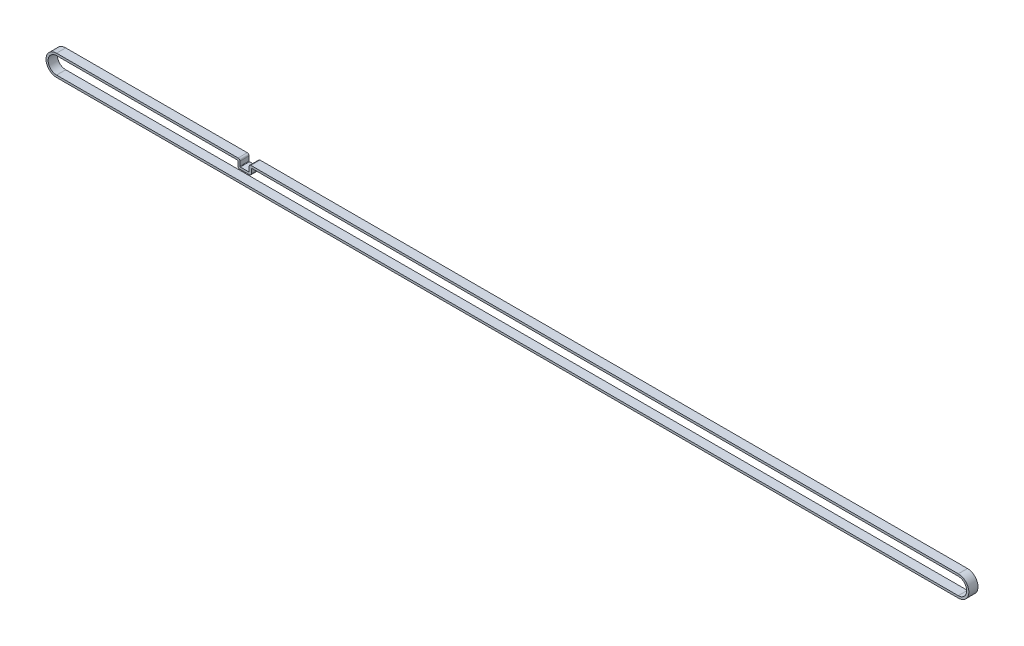
SolidWorks part; units mm, degrees
material "aluminio"
ref_plane "Alzado" through (0, 0, 0) normal (0, 0, 1) x (1, 0, 0)
ref_plane "Planta" through (0, 0, 0) normal (0, 1, 0) x (1, 0, 0)
ref_plane "Vista lateral" through (0, 0, 0) normal (1, 0, 0) x (0, 0, -1)
sketch "Croquis1" plane through (0, 0, 0) normal (0, 0, 1) x (1, 0, 0)
  line L0 (0, 0) -> (590, 0) construction
  line L1 (0, 5.5) -> (118.6, 5.5)
  line L2 (0, -5.5) -> (590, -5.5)
  line L3 (0, 6.9) -> (120, 6.9)
  line L4 (0, -6.9) -> (590, -6.9)
  line L5 (120, 6.9) -> (120, 2.5)
  line L6 (120, 2.5) -> (126, 2.5)
  line L7 (126, 2.5) -> (126, 6.9)
  line L8 (118.6, 5.5) -> (118.6, 1.1)
  line L9 (118.6, 1.1) -> (127.4, 1.1)
  line L10 (127.4, 1.1) -> (127.4, 5.5)
  line L11 (120, 5.5) -> (120, 2.5) construction
  line L12 (127.4, 5.5) -> (590, 5.5)
  line L13 (0, 5.5) -> (590, 5.5) construction
  line L14 (126, 2.5) -> (126, 5.5) construction
  line L15 (126, 6.9) -> (590, 6.9)
  line L17 (0, 6.9) -> (590, 6.9) construction
  arc A0 (0, 5.5) -> (0, -5.5) centre (0, 0) ccw
  arc A1 (590, -5.5) -> (590, 5.5) centre (590, 0) ccw
  arc A2 (590, -6.9) -> (590, 6.9) centre (590, 0) ccw
  arc A3 (0, 6.9) -> (0, -6.9) centre (0, 0) ccw
  point P3 (185, 0)
  dimension "D2" = 5.5
  dimension "D1" = 590
  dimension "D4" = 1.4
  dimension "D5" = 6
  dimension "D6" = 3
  dimension "D7" = 120
  dimension "D3" = 1.4
extrude "Saliente-Extruir1" add sketch "Croquis1" along normal blind 6
fillet "Redondeo1" radius 0.3 4 edges at (127.4, 5.5, 3) (118.6, 5.5, 3) (126, 2.5, 3) (120, 2.5, 3)
fillet "Redondeo2" radius 1.2 4 edges at (118.6, 1.1, 3) (127.4, 1.1, 3) (126, 6.9, 3) (120, 6.9, 3)
